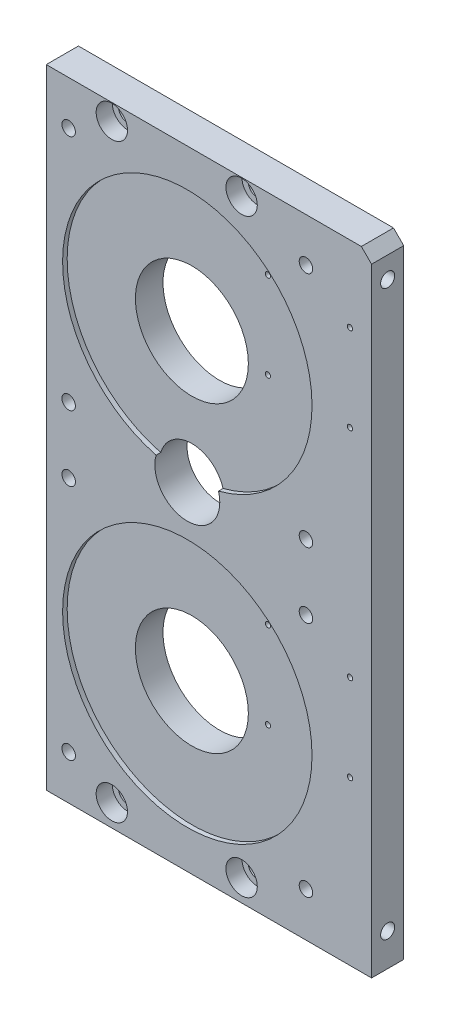
SolidWorks part; units mm, degrees
material "1060 Alloy"
ref_plane "Front Plane" through (0, 0, 0) normal (0, 0, 1) x (1, 0, 0)
ref_plane "Top Plane" through (0, 0, 0) normal (0, 1, 0) x (1, 0, 0)
ref_plane "Right Plane" through (0, 0, 0) normal (1, 0, 0) x (0, 0, -1)
sketch "Sketch1" plane through (0, 0, 0) normal (0, 0, 1) x (1, 0, 0)
  line L0 (24.8, 136.635) -> (24.8, -18.4294) construction
  line L1 (0, 184.3) -> (95.41, 184.3)
  line L2 (0, 184.3) -> (0, 0)
  line L3 (0, 0) -> (95.41, 0)
  line L4 (95.41, 184.3) -> (95.41, 0)
  line L5 (41.365, 136.635) -> (41.365, 47.785) construction
  line L6 (41.365, 153.2) -> (85.3152, 153.2) construction
  line L7 (41.365, 64.35) -> (74.3298, 64.35) construction
  line L8 (41.365, 120.07) -> (72.9436, 120.07) construction
  circle A0 centre (41.365, 136.635) radius 16.565
  circle A1 centre (41.365, 47.785) radius 16.565
  dimension "D3" = 33.13
  dimension "D1" = 184.3
  dimension "D2" = 95.41
  dimension "D4" = 24.8
  dimension "D5" = 55.72
  dimension "D6" = 31.1
extrude "Boss-Extrude1" add sketch "Sketch1" along normal blind 9.43
chamfer "Chamfer1" distance 3 angle 45 1 edges at (95.41, 184.3, 4.715)
sketch "Sketch2" plane through (0, 0, 9.43) normal (0, 0, 1) x (1, 0, 0)
  circle A0 centre (41.365, 136.635) radius 36.575
  circle A1 centre (41.365, 47.785) radius 36.575
  dimension "D1" = 73.15
extrude "Cut-Extrude1" cut sketch "Sketch2" against normal blind 1.34
sketch "Sketch3" plane through (0, 0, 9.43) normal (0, 0, 1) x (1, 0, 0)
  line L0 (41.365, 89.01) -> (41.365, 0) construction
  line L1 (0, 0) -> (95.41, 0) construction
  line L2 (31.84, 98.535) -> (0, 98.535) construction
  line L3 (0, 184.3) -> (0, 0) construction
  line L4 (41.365, 136.635) -> (41.365, 216.8632) construction
  circle A0 centre (41.365, 98.535) radius 9.525
  dimension "D1" = 19.05
  dimension "D2" = 89.01
  dimension "D3" = 31.84
extrude "Cut-Extrude2" cut sketch "Sketch3" against normal through all
sketch "Sketch4" plane through (0, 0, 9.43) normal (0, 0, 1) x (1, 0, 0)
  line L0 (19.23, 179.5) -> (19.23, 6.44) construction
  line L1 (19.23, 179.5) -> (57.29, 179.5) construction
  line L2 (57.29, 179.5) -> (57.29, 6.44) construction
  line L3 (57.29, 6.44) -> (19.23, 6.44) construction
  line L4 (16.43, 179.5) -> (16.43, 169.74) construction
  line L5 (19.23, 182.3) -> (30.5577, 182.3) construction
  line L6 (19.23, 3.64) -> (50.2126, 3.64) construction
  line L7 (92.41, 184.3) -> (0, 184.3) construction
  line L8 (0, 184.3) -> (0, 0) construction
  line L9 (22.03, 179.5) -> (22.03, 172.7217) construction
  line L10 (54.49, 179.5) -> (54.49, 171.8498) construction
  line L11 (0, 0) -> (95.41, 0) construction
  circle A0 centre (19.23, 179.5) radius 2.8
  circle A1 centre (57.29, 179.5) radius 2.8
  circle A2 centre (19.23, 6.44) radius 2.8
  circle A3 centre (57.29, 6.44) radius 2.8
  dimension "D1" = 5.6
  dimension "D2" = 2
  dimension "D3" = 16.43
  dimension "D4" = 32.46
  dimension "D5" = 3.64
extrude "Cut-Extrude3" cut sketch "Sketch4" against normal through all
sketch "Sketch5" plane through (0, 0, 9.43) normal (0, 0, 1) x (1, 0, 0)
  circle A0 centre (19.23, 179.5) radius 4.6
  circle A1 centre (57.29, 179.5) radius 4.6
  circle A2 centre (19.23, 6.44) radius 4.6
  circle A3 centre (57.29, 6.44) radius 4.6
  circle A4 centre (57.29, 6.44) radius 2.8 construction
  circle A5 centre (19.23, 6.44) radius 2.8 construction
  circle A6 centre (19.23, 179.5) radius 2.8 construction
  circle A7 centre (57.29, 179.5) radius 2.8 construction
  dimension "D1" = 9.2
extrude "Cut-Extrude4" cut sketch "Sketch5" against normal blind 4.72
sketch "Sketch6" plane through (0, 0, 9.43) normal (0, 0, 1) x (1, 0, 0)
  line L0 (6.567, 12.987) -> (76.163, 12.987) construction
  line L1 (76.163, 12.987) -> (76.163, 82.583) construction
  line L2 (76.163, 82.583) -> (6.567, 82.583) construction
  line L3 (6.567, 82.583) -> (6.567, 12.987) construction
  line L4 (41.365, 47.785) -> (41.365, 82.583) construction
  line L5 (41.365, 47.785) -> (76.163, 47.785) construction
  line L6 (6.567, 171.433) -> (6.567, 101.837) construction
  line L7 (6.567, 101.837) -> (76.163, 101.837) construction
  line L8 (76.163, 101.837) -> (76.163, 171.433) construction
  line L9 (76.163, 171.433) -> (6.567, 171.433) construction
  line L10 (41.365, 136.635) -> (76.163, 136.635) construction
  line L11 (41.365, 136.635) -> (41.365, 171.433) construction
  circle A0 centre (6.567, 171.433) radius 1.98
  circle A1 centre (76.163, 171.433) radius 1.98
  circle A2 centre (76.163, 101.837) radius 1.98
  circle A3 centre (6.567, 101.837) radius 1.98
  circle A4 centre (6.567, 82.583) radius 1.98
  circle A5 centre (76.163, 82.583) radius 1.98
  circle A6 centre (76.163, 12.987) radius 1.98
  circle A7 centre (6.567, 12.987) radius 1.98
  dimension "D2" = 3.96
  dimension "D1" = 69.596
extrude "Cut-Extrude5" cut sketch "Sketch6" against normal through all
sketch "Sketch7" plane through (95.41, 0, 0) normal (1, 0, 0) x (0, 0, -1)
  line L0 (-4.715, 175.02) -> (-4.715, 9.6) construction
  line L1 (-9.43, 0) -> (-9.43, 181.3) construction
  line L2 (0, 0) -> (0, 181.3) construction
  line L3 (-4.715, 7.54) -> (-4.715, 0) construction
  line L4 (-9.43, 0) -> (0, 0) construction
  line L5 (-4.715, 172.96) -> (0, 172.96) construction
  line L7 (-4.715, 11.66) -> (0, 11.66) construction
  circle A0 centre (-4.715, 175.02) radius 2.06
  circle A1 centre (-4.715, 9.6) radius 2.06
  dimension "D1" = 4.12
  dimension "D2" = 7.54
  dimension "D3" = 161.3
extrude "Cut-Extrude6" cut sketch "Sketch7" against normal blind 6.93
sketch "Sketch9" plane through (0, 0, 0) normal (0, 0, -1) x (-1, 0, 0)
  line L0 (-89.08, 73.185) -> (-89.08, 47.785) construction
  line L1 (-89.08, 47.785) -> (-63.68, 47.785) construction
  line L2 (-63.68, 47.785) -> (-63.68, 73.185) construction
  line L3 (-63.68, 73.185) -> (-89.08, 73.185) construction
  line L4 (-89.08, 162.035) -> (-89.08, 136.635) construction
  line L5 (-89.08, 136.635) -> (-63.68, 136.635) construction
  line L6 (-63.68, 136.635) -> (-63.68, 162.035) construction
  line L7 (-63.68, 162.035) -> (-89.08, 162.035) construction
  line L8 (-89.85, 162.035) -> (-89.85, 136.635) construction
  line L9 (-88.31, 136.635) -> (-88.31, 162.035) construction
  line L10 (-89.08, 162.805) -> (-63.68, 162.805) construction
  line L11 (-64.45, 162.035) -> (-64.45, 136.635) construction
  line L12 (-95.41, 0) -> (-95.41, 181.3) construction
  line L14 (-63.68, 136.635) -> (-41.365, 136.635) construction
  line L15 (-63.68, 47.785) -> (-41.365, 47.785) construction
  circle A0 centre (-89.08, 162.035) radius 0.77
  circle A1 centre (-63.68, 162.035) radius 0.77
  circle A2 centre (-89.08, 136.635) radius 0.77
  circle A3 centre (-63.68, 136.635) radius 0.77
  circle A4 centre (-89.08, 73.185) radius 0.77
  circle A5 centre (-63.68, 73.185) radius 0.77
  circle A6 centre (-89.08, 47.785) radius 0.77
  circle A7 centre (-63.68, 47.785) radius 0.77
  circle A8 centre (-41.365, 136.635) radius 16.565 construction
  circle A9 centre (-41.365, 47.785) radius 16.565 construction
  dimension "D1" = 1.54
  dimension "D2" = 5.56
  dimension "D3" = 25.4
extrude "Cut-Extrude7" cut sketch "Sketch9" against normal through all
